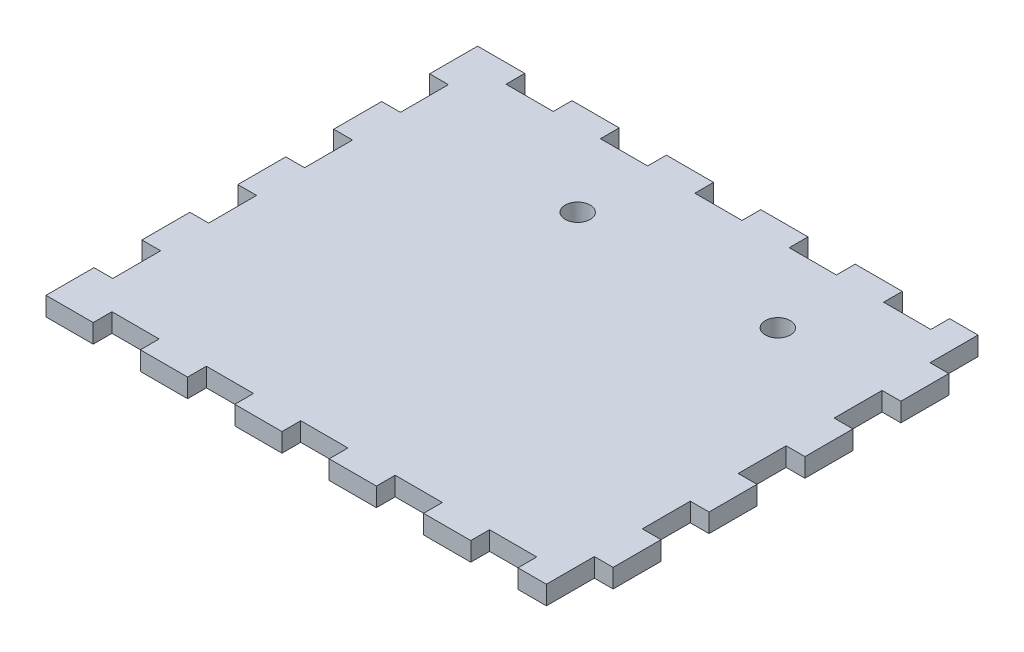
SolidWorks part; units mm, degrees
ref_plane "Front" through (0, 0, 0) normal (0, 0, 1) x (1, 0, 0)
ref_plane "Top" through (0, 0, 0) normal (0, 1, 0) x (1, 0, 0)
ref_plane "Right" through (0, 0, 0) normal (1, 0, 0) x (0, 0, -1)
sketch "Skizze1" plane through (0, 0, 0) normal (0, 1, 0) x (1, 0, 0)
  line L0 (0, 0.0001) -> (7.5446, 0.0001)
  line L5 (0, 0) -> (83, 0) construction
  line L6 (0, 0) -> (0, 69) construction
  line L7 (0, 69) -> (83, 69) construction
  line L8 (83, 0) -> (83, 69) construction
  line L9 (7.5446, 3.0001) -> (7.5446, 0.0001)
  line L10 (7.5446, 3.0001) -> (15.0909, 3.0001)
  line L11 (15.0909, 3.0001) -> (15.0909, 0.0001)
  line L12 (15.0909, 0.0001) -> (22.6357, 0.0001)
  line L13 (22.6357, 3.0001) -> (22.6357, 0.0001)
  line L14 (22.6357, 3.0001) -> (30.1816, 3.0001)
  line L15 (30.1816, 3.0001) -> (30.1816, 0.0001)
  line L16 (30.1816, 0.0001) -> (37.7264, 0.0001)
  line L17 (37.7264, 3.0001) -> (37.7264, 0.0001)
  line L18 (37.7264, 3.0001) -> (45.2727, 3.0001)
  line L19 (45.2727, 3.0001) -> (45.2727, 0.0001)
  line L20 (45.2727, 0.0001) -> (52.818, 0.0001)
  line L21 (52.818, 3.0001) -> (52.818, 0.0001)
  line L22 (52.818, 3.0001) -> (60.3644, 3.0001)
  line L23 (60.3644, 3.0001) -> (60.3644, 0.0001)
  line L24 (60.3644, 0.0001) -> (67.9082, 0.0001)
  line L25 (67.9082, 3.0001) -> (67.9082, 0.0001)
  line L26 (67.9082, 3.0001) -> (75.4545, 3.0001)
  line L27 (75.4545, 3.0001) -> (75.4545, 0.0001)
  line L28 (75.4545, 0.0001) -> (79.9986, 0.0001)
  line L29 (0, 69) -> (7.5446, 69)
  line L30 (7.5446, 69) -> (7.5446, 66)
  line L31 (7.5446, 66) -> (15.0909, 66)
  line L32 (15.0909, 69) -> (15.0909, 66)
  line L33 (15.0909, 69) -> (22.6357, 69)
  line L34 (22.6357, 69) -> (22.6357, 66)
  line L35 (22.6357, 66) -> (30.1816, 66)
  line L36 (30.1816, 69) -> (30.1816, 66)
  line L37 (30.1816, 69) -> (37.7264, 69)
  line L38 (37.7264, 69) -> (37.7264, 66)
  line L39 (37.7264, 66) -> (45.2727, 66)
  line L40 (45.2727, 69) -> (45.2727, 66)
  line L41 (45.2727, 69) -> (52.818, 69)
  line L42 (52.818, 69) -> (52.818, 66)
  line L43 (52.818, 66) -> (60.3644, 66)
  line L44 (60.3644, 69) -> (60.3644, 66)
  line L45 (60.3644, 69) -> (67.9082, 69)
  line L46 (67.9082, 69) -> (67.9082, 66)
  line L47 (67.9082, 66) -> (75.4545, 66)
  line L48 (75.4545, 69) -> (75.4545, 66)
  line L49 (75.4545, 69) -> (79.9986, 69)
  line L50 (0, 0.0001) -> (0, 7.6664)
  line L51 (2.9997, 7.6664) -> (0, 7.6664)
  line L52 (2.9997, 7.6664) -> (2.9997, 15.3321)
  line L53 (2.9997, 15.3321) -> (0, 15.3321)
  line L54 (0, 15.3321) -> (0, 22.9993)
  line L55 (2.9997, 22.9993) -> (0, 22.9993)
  line L56 (2.9997, 22.9993) -> (2.9997, 30.6656)
  line L57 (2.9997, 30.6656) -> (0, 30.6656)
  line L58 (0, 30.6656) -> (0, 38.3331)
  line L59 (2.9997, 38.3331) -> (0, 38.3331)
  line L60 (2.9997, 38.3331) -> (2.9997, 45.999)
  line L61 (2.9997, 45.999) -> (0, 45.999)
  line L62 (0, 45.999) -> (0, 53.6665)
  line L63 (2.9997, 53.6665) -> (0, 53.6665)
  line L64 (2.9997, 53.6665) -> (2.9997, 61.3325)
  line L65 (2.9997, 61.3325) -> (0, 61.3325)
  line L66 (0, 61.3325) -> (0, 69)
  line L67 (79.9986, 0.0001) -> (79.9986, 7.6664)
  line L68 (82.9983, 7.6664) -> (79.9986, 7.6664)
  line L69 (82.9983, 7.6664) -> (82.9983, 15.3321)
  line L70 (82.9983, 15.3321) -> (79.9986, 15.3321)
  line L71 (79.9986, 15.3321) -> (79.9986, 22.9993)
  line L72 (82.9983, 22.9993) -> (79.9986, 22.9993)
  line L73 (82.9983, 22.9993) -> (82.9983, 30.6656)
  line L74 (82.9983, 30.6656) -> (79.9986, 30.6656)
  line L75 (79.9986, 30.6656) -> (79.9986, 38.3331)
  line L76 (82.9983, 38.3331) -> (79.9986, 38.3331)
  line L77 (82.9983, 38.3331) -> (82.9983, 45.999)
  line L78 (82.9983, 45.999) -> (79.9986, 45.999)
  line L79 (79.9986, 45.999) -> (79.9986, 53.6665)
  line L80 (82.9983, 53.6665) -> (79.9986, 53.6665)
  line L81 (82.9983, 53.6665) -> (82.9983, 61.3325)
  line L82 (82.9983, 61.3325) -> (79.9986, 61.3325)
  line L83 (79.9986, 61.3325) -> (79.9986, 69)
  dimension "D1" = 69
  dimension "D2" = 83
extrude "Aufsatz-Linear austragen1" add sketch "Skizze1" along normal blind 3
sketch "Skizze2" plane through (0, 0, 0) normal (0, -1, 0) x (1, 0, 0)
  line L0 (79.9986, -30.6656) -> (79.9986, -38.3331) construction
  line L1 (75.4545, -66) -> (67.9082, -66) construction
  circle A0 centre (62.9986, -54) radius 2
  circle A1 centre (30.9986, -54) radius 2
  dimension "D1" = 17
  dimension "D3" = 4
  dimension "D5" = 32
  dimension "D2" = 12
  dimension "D4" = 2
extrude "Schnitt-Linear austragen1" cut sketch "Skizze2" against normal blind 3
sketch "Skizze3" [suppressed] plane through (0, 0, 0) normal (0, -1, 0) x (1, 0, 0)
  line L0 (2.9997, -61.3325) -> (2.9997, -53.6665) construction
  line L3 (15.0909, -66) -> (7.5446, -66) construction
  circle A0 centre (51.9997, -54) radius 2
  circle A1 centre (19.9997, -54) radius 2
  dimension "D1" = 4
  dimension "D2" = 32
  dimension "D3" = 17
  dimension "D4" = 12
extrude "Schnitt-Linear austragen2" [suppressed] cut sketch "Skizze3" against normal blind 3
